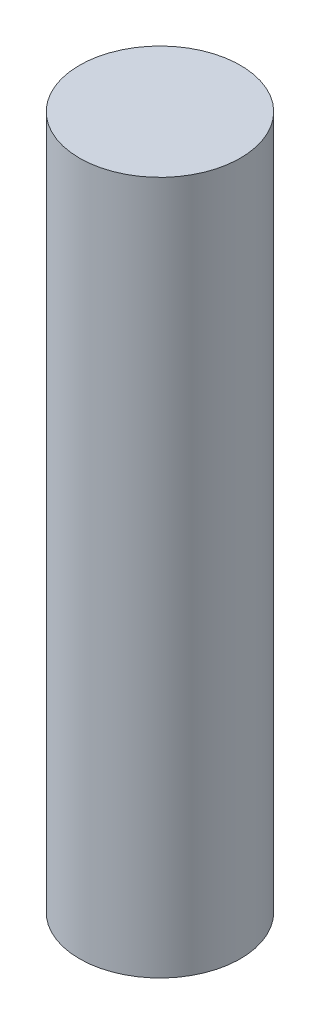
SolidWorks part; units mm, degrees
ref_plane "Front Plane" through (0, 0, 0) normal (0, 0, 1) x (1, 0, 0)
ref_plane "Top Plane" through (0, 0, 0) normal (0, 1, 0) x (1, 0, 0)
ref_plane "Right Plane" through (0, 0, 0) normal (1, 0, 0) x (0, 0, -1)
sketch "Sketch1" plane through (0, 0, 0) normal (0, 1, 0) x (1, 0, 0)
  circle A0 centre (0, 0) radius 10
extrude "Boss-Extrude1" add sketch "Sketch1" along normal blind 86.19
